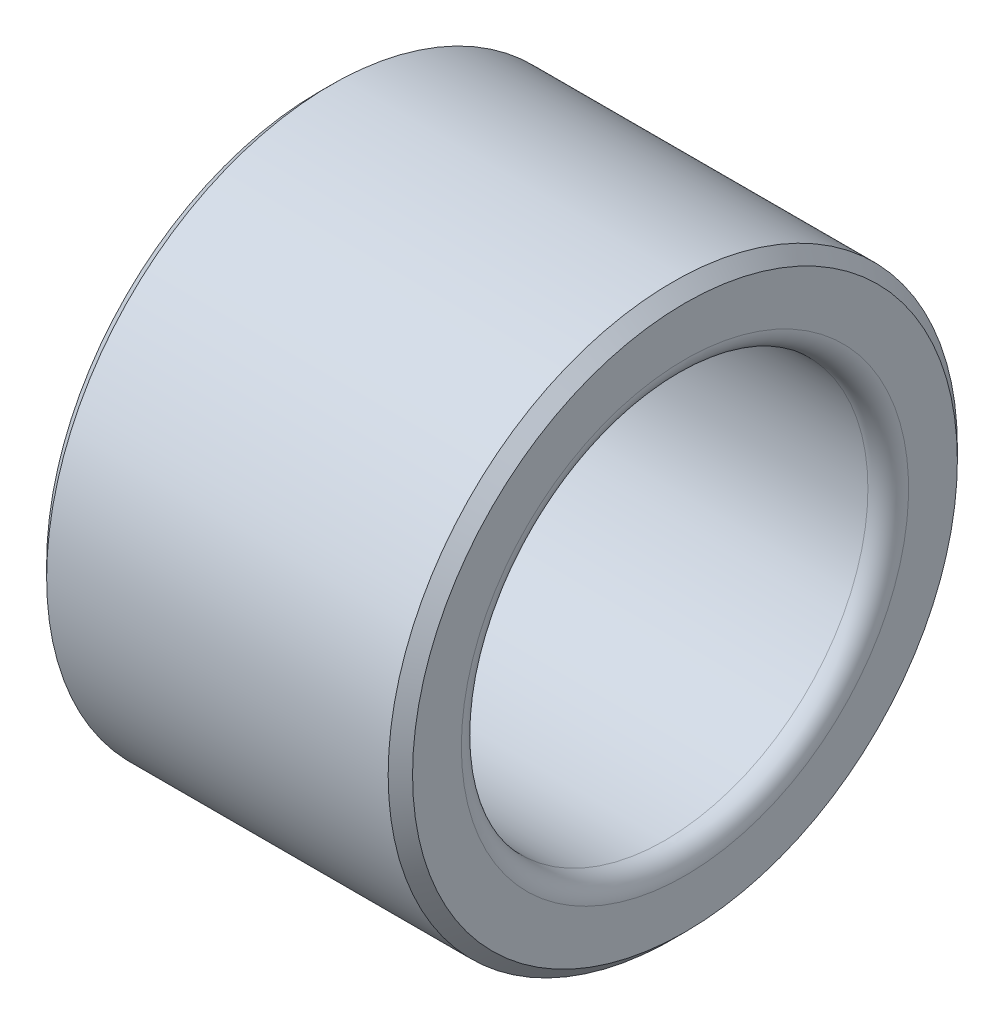
SolidWorks part; units mm, degrees
ref_plane "前基準面" through (0, 0, 0) normal (0, 0, 1) x (1, 0, 0)
ref_plane "上基準面" through (0, 0, 0) normal (0, 1, 0) x (1, 0, 0)
ref_plane "右基準面" through (0, 0, 0) normal (1, 0, 0) x (0, 0, -1)
sketch "草圖1" plane through (0, 0, 0) normal (0, 0, 1) x (1, 0, 0)
  line L0 (-51.5237, 0) -> (51.0894, 0) construction
  line L2 (-4.5, 5) -> (4.5, 5)
  line L3 (-4.5, 5) -> (-4.5, 7)
  line L4 (-4.5, 7) -> (4.5, 7)
  line L5 (4.5, 5) -> (4.5, 7)
  point P7 (0, 5)
  dimension "D1" = 14
  dimension "D2" = 10
  dimension "D3" = 9
revolve "旋轉1" add sketch "草圖1" angle 360 about L0
chamfer "導角1" distance 0.3 angle 45 2 edges at (-4.5, 0, 7) (4.5, 0, 7)
fillet "圓角1" radius 0.5 2 edges at (-4.5, 0, 5) (4.5, 0, 5)
